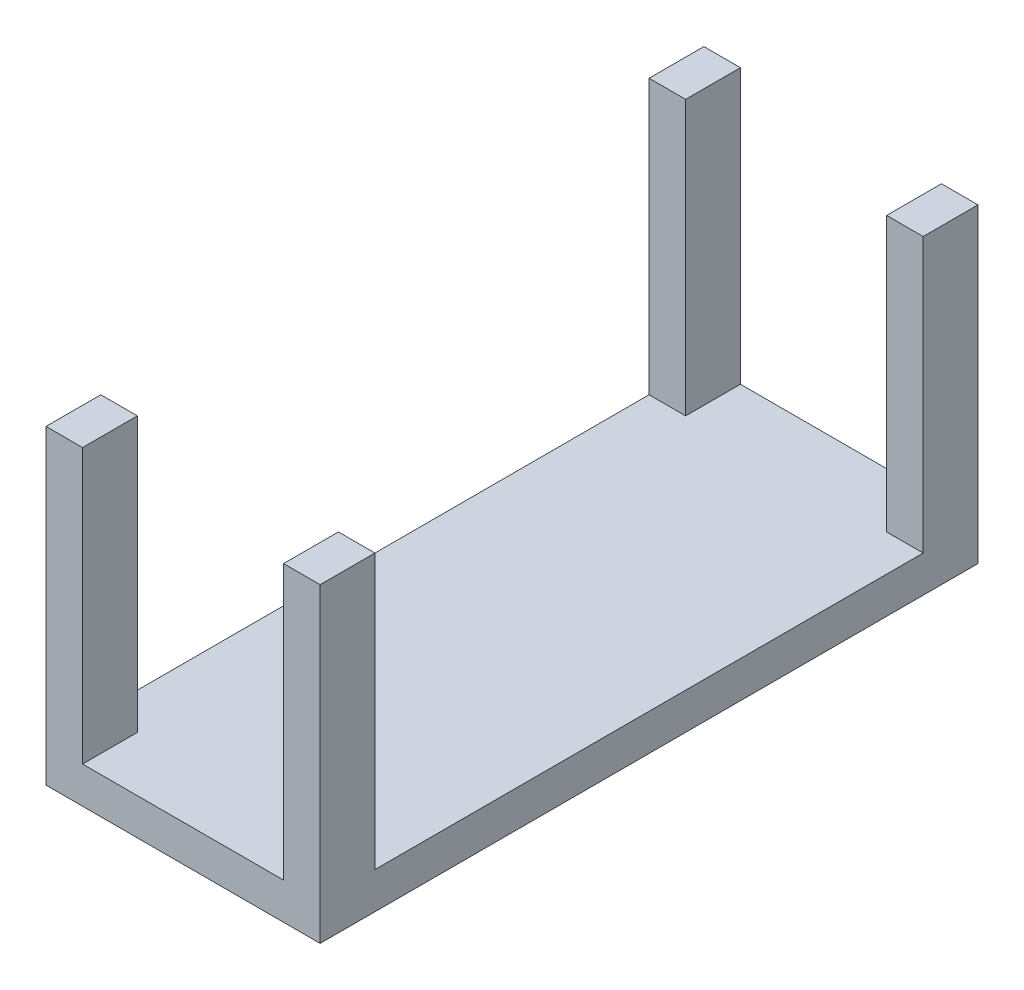
SolidWorks part; units mm, degrees
ref_plane "Front Plane" through (0, 0, 0) normal (0, 0, 1) x (1, 0, 0)
ref_plane "Top Plane" through (0, 0, 0) normal (0, 1, 0) x (1, 0, 0)
ref_plane "Right Plane" through (0, 0, 0) normal (1, 0, 0) x (0, 0, -1)
sketch "Sketch1" plane through (0, 0, 0) normal (0, 0, 1) x (1, 0, 0)
  line L1 (7.5, -8.5) -> (-7.5, -8.5)
  line L2 (7.5, -8.5) -> (7.5, 8.5)
  line L3 (7.5, 8.5) -> (-7.5, 8.5)
  line L4 (-7.5, -8.5) -> (-7.5, 8.5)
  line L5 (7.5, -8.5) -> (-7.5, 8.5) construction
  line L6 (7.5, 8.5) -> (-7.5, -8.5) construction
  point P0 (0, 0)
  dimension "D1" = 15
  dimension "D2" = 17
extrude "Boss-Extrude1" add sketch "Sketch1" along normal blind 36
sketch "Sketch2" plane through (0, 8.5, 0) normal (0, 1, 0) x (1, 0, 0)
  line L0 (-7.5, -36) -> (-7.5, 0) construction
  line L1 (5.5, -36) -> (-5.5, -36)
  line L2 (5.5, -36) -> (5.5, 0)
  line L3 (5.5, 0) -> (-5.5, 0)
  line L4 (-5.5, -36) -> (-5.5, 0)
  line L5 (5.5, -36) -> (-5.5, 0) construction
  line L6 (5.5, 0) -> (-5.5, -36) construction
  line L7 (7.5, -36) -> (7.5, 0) construction
  line L9 (7.5, 0) -> (-7.5, 0) construction
  line L10 (7.5, -36) -> (-7.5, -36) construction
  point P0 (0, -18)
  dimension "D1" = 2
  dimension "D2" = 2
extrude "Cut-Extrude1" cut sketch "Sketch2" against normal blind 15
sketch "Sketch3" plane through (0, 8.5, 0) normal (0, 1, 0) x (1, 0, 0)
  line L1 (7.5, -3) -> (7.5, -33)
  line L2 (-7.5, -33) -> (-7.5, -3)
  line L3 (-7.5, -33) -> (7.5, -33)
  line L5 (7.5, -36) -> (7.5, 0) construction
  line L8 (7.5, -3) -> (7.5, 0) construction
  line L9 (-7.5, -36) -> (-7.5, 0) construction
  line L10 (-7.5, -3) -> (7.5, -3)
  line L11 (7.5, -36) -> (7.5, -33) construction
  dimension "D1" = 30
extrude "Cut-Extrude2" cut sketch "Sketch3" against normal blind 15
